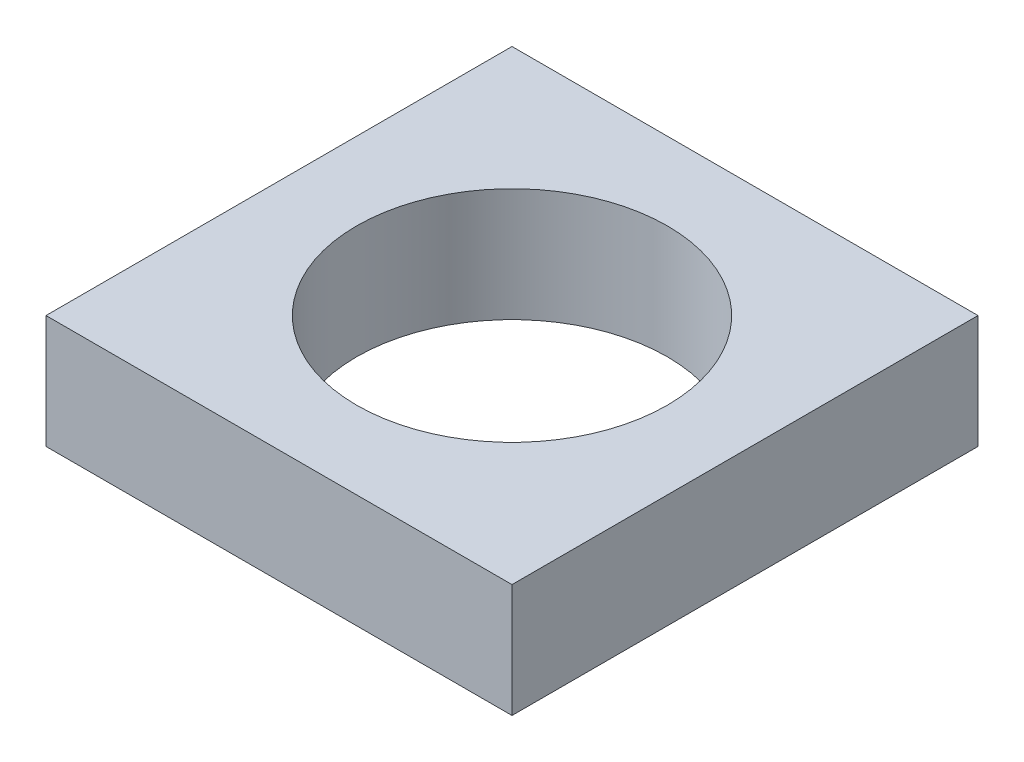
SolidWorks part; units mm, degrees
ref_plane "Front Plane" through (0, 0, 0) normal (0, 0, 1) x (1, 0, 0)
ref_plane "Top Plane" through (0, 0, 0) normal (0, 1, 0) x (1, 0, 0)
ref_plane "Right Plane" through (0, 0, 0) normal (1, 0, 0) x (0, 0, -1)
sketch "Sketch1" plane through (0, 0, 0) normal (0, 1, 0) x (1, 0, 0)
  line L1 (-30, -30) -> (30, -30)
  line L2 (-30, -30) -> (-30, 30)
  line L3 (-30, 30) -> (30, 30)
  line L4 (30, -30) -> (30, 30)
  line L5 (-30, -30) -> (30, 30) construction
  line L6 (-30, 30) -> (30, -30) construction
  circle A0 centre (0, 0) radius 20
  point P0 (0, 0)
  dimension "D1" = 40
  dimension "D2" = 60
  dimension "D3" = 60
extrude "Boss-Extrude1" add sketch "Sketch1" along normal blind 14.6
